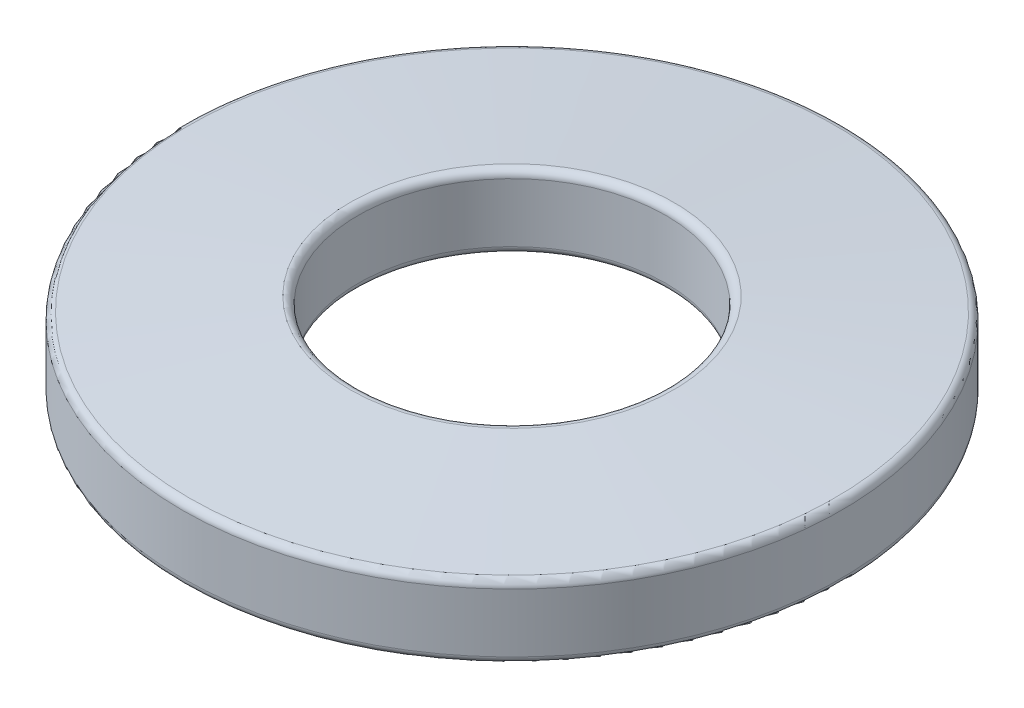
SolidWorks part; units mm, degrees
ref_plane "Front Plane" through (0, 0, 0) normal (0, 0, 1) x (1, 0, 0)
ref_plane "Top Plane" through (0, 0, 0) normal (0, 1, 0) x (1, 0, 0)
ref_plane "Right Plane" through (0, 0, 0) normal (1, 0, 0) x (0, 0, -1)
sketch "Sketch2" plane through (0, 0, 0) normal (1, 0, 0) x (0, 0, -1)
  line L0 (-5.3213, 0) -> (5.3213, 0) construction
  line L1 (5.3213, 3.048) -> (5.3213, 0.508)
  line L2 (5.3213, 0) -> (11.3792, 0) construction
  line L3 (5.3213, 0) -> (5.3213, 3.048) construction
  line L4 (5.3213, 3.048) -> (11.3792, 3.048) construction
  line L5 (11.3792, 0) -> (11.3792, 3.048) construction
  line L6 (11.3792, 0) -> (11.3792, 2.54)
  line L7 (5.3213, 3.048) -> (11.3792, 2.54)
  line L8 (11.3792, 0) -> (5.3213, 0.508)
  line L9 (0, 0) -> (0, 11.9435) construction
  point P4 (0, 0)
  dimension "D1" = 10.6426
  dimension "D2" = 6.0579
  dimension "D3" = 3.048
  dimension "D4" = 2.54
  dimension "D5" = 2.54
revolve "Revolve1" add sketch "Sketch2" angle 360 about L9
fillet "Fillet1" radius 0.254 4 edges at (0, 0, -11.3792) (0, 2.54, -11.3792) (0, 0.508, -5.3213) (0, 3.048, -5.3213)
